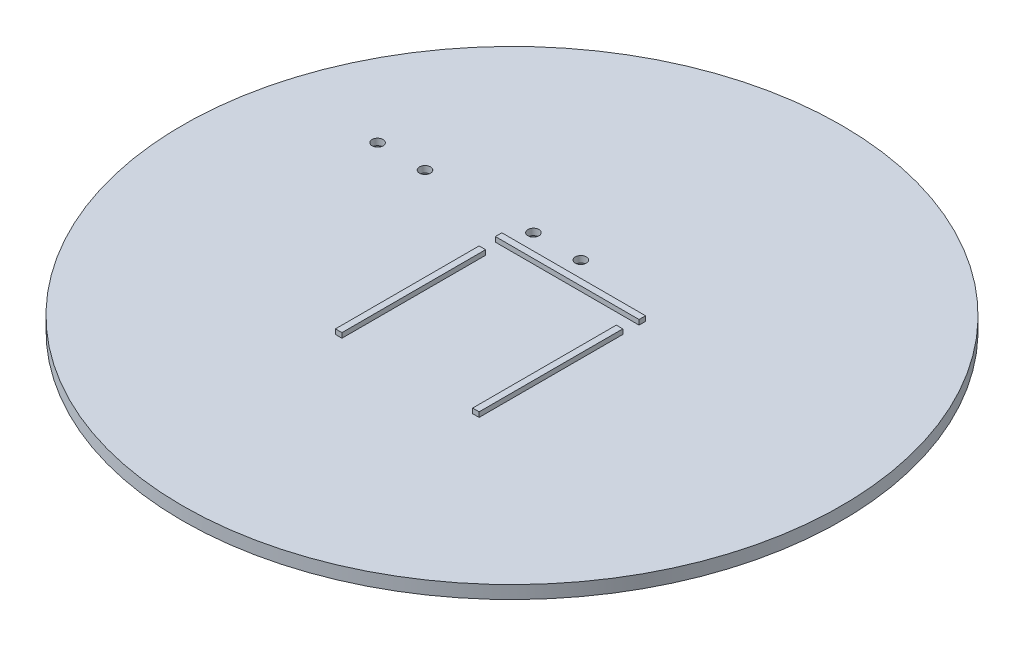
SolidWorks part; units mm, degrees
ref_plane "Front Plane" through (0, 0, 0) normal (0, 0, 1) x (1, 0, 0)
ref_plane "Top Plane" through (0, 0, 0) normal (0, 1, 0) x (1, 0, 0)
ref_plane "Right Plane" through (0, 0, 0) normal (1, 0, 0) x (0, 0, -1)
sketch "Sketch2" plane through (0, 0, 0) normal (0, 1, 0) x (1, 0, 0)
  circle A0 centre (0, 0) radius 101.5
  dimension "D1" = 203
extrude "Boss-Extrude2" add sketch "Sketch2" along normal mid plane 4
sketch "Sketch4" plane through (0, 2, 0) normal (0, 1, 0) x (1, 0, 0)
  line L13 (-22.125, 19) -> (22.125, 19)
  line L14 (-22.125, 19) -> (-22.125, 17)
  line L15 (-22.125, 17) -> (22.125, 17)
  line L16 (22.125, 19) -> (22.125, 17)
  line L17 (-22.125, 12) -> (-20.125, 12)
  line L18 (-22.125, 12) -> (-22.125, -32.25)
  line L19 (-22.125, -32.25) -> (-20.125, -32.25)
  line L20 (-20.125, 12) -> (-20.125, -32.25)
  line L21 (20.125, 12) -> (22.125, 12)
  line L22 (20.125, 12) -> (20.125, -32.25)
  line L23 (20.125, -32.25) -> (22.125, -32.25)
  line L24 (22.125, 12) -> (22.125, -32.25)
  point P12 (0, 17)
  dimension "D1" = 44.25
  dimension "D2" = 5
  dimension "D3" = 2
  dimension "D4" = 17
extrude "Boss-Extrude3" add sketch "Sketch4" along normal mid plane 3
sketch "Sketch5" plane through (0, 2, 0) normal (0, 1, 0) x (1, 0, 0)
  circle A0 centre (-66.8, 25.4) radius 1.7
  circle A1 centre (0, 0) radius 101.5 construction
  circle A2 centre (0, 0) radius 101.3787 construction
  circle A3 centre (-52.2, 25.4) radius 1.7
  circle A4 centre (-18.8, 25.4) radius 1.7
  circle A5 centre (-4.2, 25.4) radius 1.7
  dimension "D3" = 3.4
  dimension "D1" = 66.8
  dimension "D2" = 25.4
extrude "Cut-Extrude1" cut sketch "Sketch5" against normal through all
sketch "Sketch6" plane through (0, -2, 0) normal (0, -1, 0) x (-1, 0, 0)
  line L1 (7.4909, 25.4) -> (5.8454, 28.25)
  line L2 (5.8454, 28.25) -> (2.5546, 28.25)
  line L3 (2.5546, 28.25) -> (0.9091, 25.4)
  line L4 (0.9091, 25.4) -> (2.5546, 22.55)
  line L5 (2.5546, 22.55) -> (5.8454, 22.55)
  line L6 (5.8454, 22.55) -> (7.4909, 25.4)
  line L7 (22.0909, 25.4) -> (20.4454, 28.25)
  line L8 (20.4454, 28.25) -> (17.1546, 28.25)
  line L9 (17.1546, 28.25) -> (15.5091, 25.4)
  line L10 (15.5091, 25.4) -> (17.1546, 22.55)
  line L11 (17.1546, 22.55) -> (20.4454, 22.55)
  line L12 (20.4454, 22.55) -> (22.0909, 25.4)
  line L13 (55.4909, 25.4) -> (53.8454, 28.25)
  line L14 (53.8454, 28.25) -> (50.5546, 28.25)
  line L15 (50.5546, 28.25) -> (48.9091, 25.4)
  line L16 (48.9091, 25.4) -> (50.5546, 22.55)
  line L17 (50.5546, 22.55) -> (53.8454, 22.55)
  line L18 (53.8454, 22.55) -> (55.4909, 25.4)
  line L19 (70.0909, 25.4) -> (68.4454, 28.25)
  line L20 (68.4454, 28.25) -> (65.1546, 28.25)
  line L21 (65.1546, 28.25) -> (63.5091, 25.4)
  line L22 (63.5091, 25.4) -> (65.1546, 22.55)
  line L23 (65.1546, 22.55) -> (68.4454, 22.55)
  line L24 (68.4454, 22.55) -> (70.0909, 25.4)
  circle A0 centre (4.2, 25.4) radius 2.85 construction
  circle A1 centre (18.8, 25.4) radius 2.85 construction
  circle A2 centre (52.2, 25.4) radius 2.85 construction
  circle A3 centre (66.8, 25.4) radius 2.85 construction
  dimension "D1" = 5.7
extrude "Cut-Extrude2" cut sketch "Sketch6" against normal blind 2
